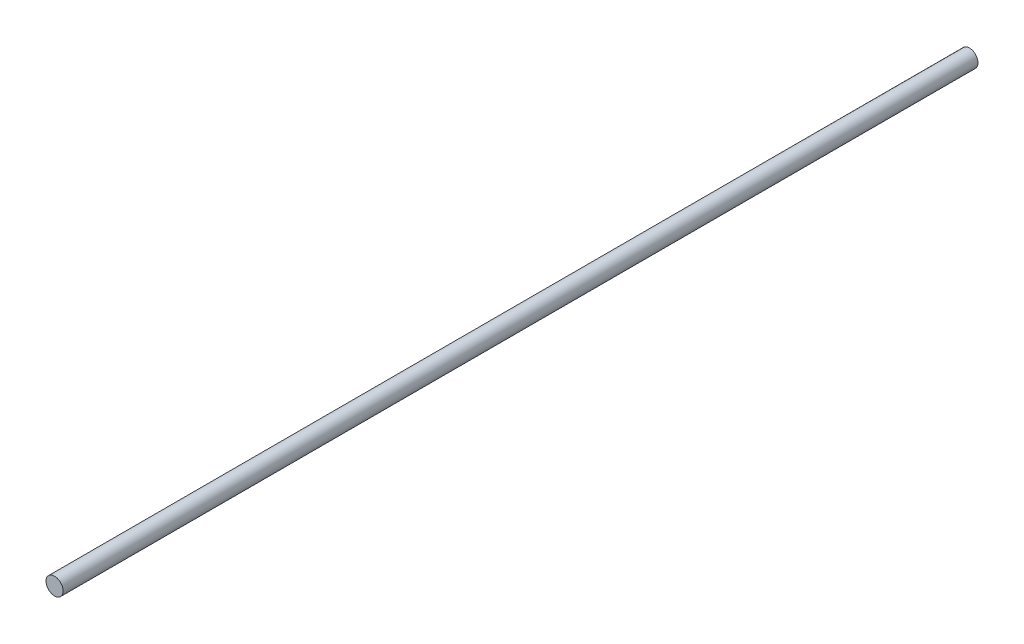
SolidWorks part; units mm, degrees
material "Aço cromo inoxidável"
ref_plane "Plano frontal" through (0, 0, 0) normal (0, 0, 1) x (1, 0, 0)
ref_plane "Plano superior" through (0, 0, 0) normal (0, 1, 0) x (1, 0, 0)
ref_plane "Plano direito" through (0, 0, 0) normal (1, 0, 0) x (0, 0, -1)
sketch "Esboço1" plane through (0, 0, 0) normal (0, 0, 1) x (1, 0, 0)
  circle A0 centre (0, 0) radius 1.5
  dimension "D1" = 3
extrude "Ressalto-extrusão1" add sketch "Esboço1" along normal blind 160
